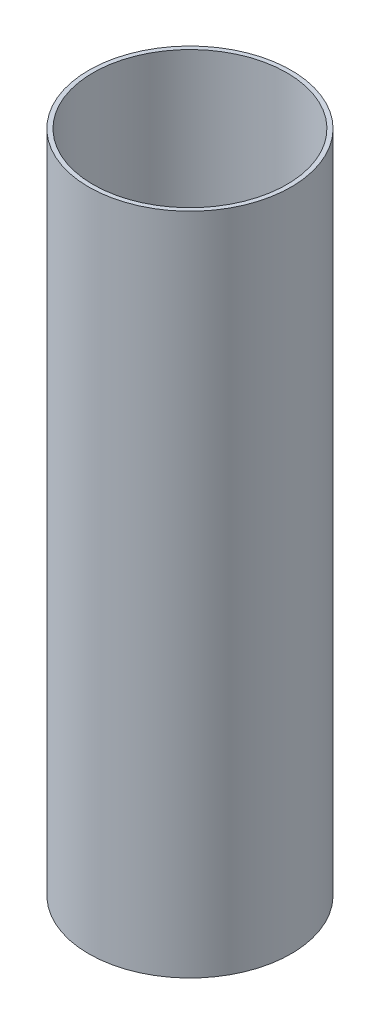
SolidWorks part; units mm, degrees
ref_plane "Front Plane" through (0, 0, 0) normal (0, 0, 1) x (1, 0, 0)
ref_plane "Top Plane" through (0, 0, 0) normal (0, 1, 0) x (1, 0, 0)
ref_plane "Right Plane" through (0, 0, 0) normal (1, 0, 0) x (0, 0, -1)
sketch "Sketch1" plane through (0, 0, 0) normal (0, 1, 0) x (1, 0, 0)
  circle A0 centre (0, 0) radius 76.2
  circle A1 centre (0, 0) radius 72.95
  dimension "D1" = 152.4
  dimension "D2" = 3.25
extrude "Boss-Extrude1" add sketch "Sketch1" along normal blind 500
